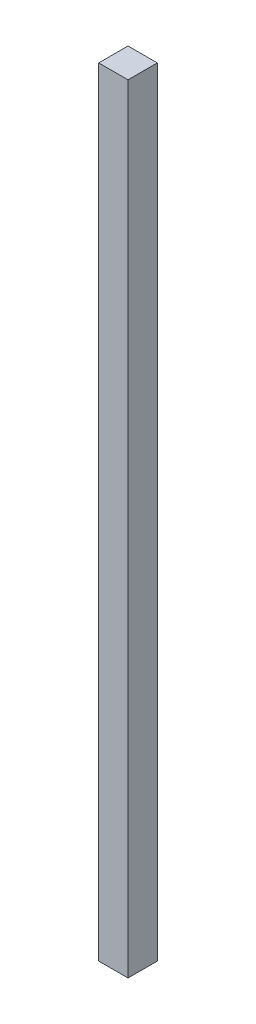
SolidWorks part; units mm, degrees
ref_plane "Front Plane" through (0, 0, 0) normal (0, 0, 1) x (1, 0, 0)
ref_plane "Top Plane" through (0, 0, 0) normal (0, 1, 0) x (1, 0, 0)
ref_plane "Right Plane" through (0, 0, 0) normal (1, 0, 0) x (0, 0, -1)
sketch "Sketch1" plane through (0, 0, 0) normal (0, 1, 0) x (1, 0, 0)
  line L1 (0, 3.2) -> (3.2, 3.2)
  line L2 (0, 3.2) -> (0, 0)
  line L3 (0, 0) -> (3.2, 0)
  line L4 (3.2, 3.2) -> (3.2, 0)
  point P4 (0, 0)
  dimension "D1" = 3.2
  dimension "D2" = 3.2
extrude "Boss-Extrude1" add sketch "Sketch1" along normal blind 85 contours L2 L3 L4 L1
